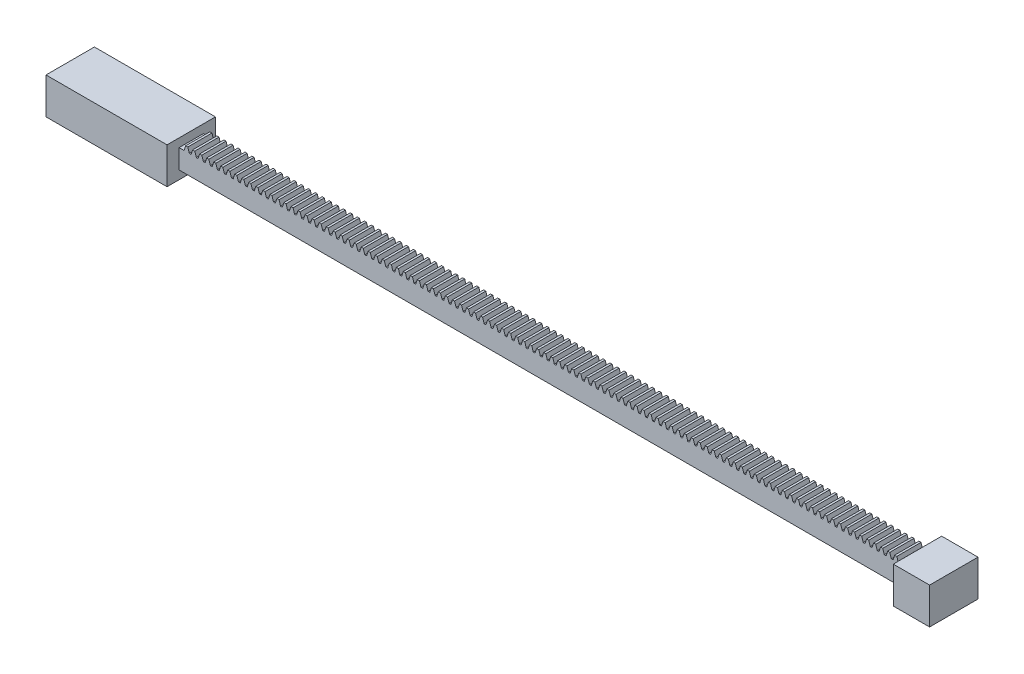
SolidWorks part; units mm, degrees
ref_plane "Front Plane" through (0, 0, 0) normal (0, 0, 1) x (1, 0, 0)
ref_plane "Top Plane" through (0, 0, 0) normal (0, 1, 0) x (1, 0, 0)
ref_plane "Right Plane" through (0, 0, 0) normal (1, 0, 0) x (0, 0, -1)
sketch "Sketch1" plane through (0, 0, 0) normal (0, 0, 1) x (1, 0, 0)
  line L0 (147.8394, 4) -> (148.4797, 6)
  line L1 (-150, 4) -> (150, 4)
  line L2 (-150, 4) -> (-150, -4)
  line L3 (-150, -4) -> (150, -4)
  line L4 (150, 4) -> (150, -4)
  line L5 (-150, 4) -> (150, -4) construction
  line L6 (-150, -4) -> (150, 4) construction
  line L7 (148.4797, 6) -> (149.3597, 6)
  line L8 (149.3597, 6) -> (150, 4)
  line L9 (144.9394, 4) -> (145.5797, 6)
  line L10 (145.5797, 6) -> (146.4597, 6)
  line L11 (146.4597, 6) -> (147.1, 4)
  line L12 (142.0394, 4) -> (142.6797, 6)
  line L13 (142.6797, 6) -> (143.5597, 6)
  line L14 (143.5597, 6) -> (144.2, 4)
  line L15 (139.1394, 4) -> (139.7797, 6)
  line L16 (139.7797, 6) -> (140.6597, 6)
  line L17 (140.6597, 6) -> (141.3, 4)
  line L18 (136.2394, 4) -> (136.8797, 6)
  line L19 (136.8797, 6) -> (137.7597, 6)
  line L20 (137.7597, 6) -> (138.4, 4)
  line L21 (133.3394, 4) -> (133.9797, 6)
  line L22 (133.9797, 6) -> (134.8597, 6)
  line L23 (134.8597, 6) -> (135.5, 4)
  line L24 (130.4394, 4) -> (131.0797, 6)
  line L25 (131.0797, 6) -> (131.9597, 6)
  line L26 (131.9597, 6) -> (132.6, 4)
  line L27 (127.5394, 4) -> (128.1797, 6)
  line L28 (128.1797, 6) -> (129.0597, 6)
  line L29 (129.0597, 6) -> (129.7, 4)
  line L30 (124.6394, 4) -> (125.2797, 6)
  line L31 (125.2797, 6) -> (126.1597, 6)
  line L32 (126.1597, 6) -> (126.8, 4)
  line L33 (121.7394, 4) -> (122.3797, 6)
  line L34 (122.3797, 6) -> (123.2597, 6)
  line L35 (123.2597, 6) -> (123.9, 4)
  line L36 (118.8394, 4) -> (119.4797, 6)
  line L37 (119.4797, 6) -> (120.3597, 6)
  line L38 (120.3597, 6) -> (121, 4)
  line L39 (115.9394, 4) -> (116.5797, 6)
  line L40 (116.5797, 6) -> (117.4597, 6)
  line L41 (117.4597, 6) -> (118.1, 4)
  line L42 (113.0394, 4) -> (113.6797, 6)
  line L43 (113.6797, 6) -> (114.5597, 6)
  line L44 (114.5597, 6) -> (115.2, 4)
  line L45 (110.1394, 4) -> (110.7797, 6)
  line L46 (110.7797, 6) -> (111.6597, 6)
  line L47 (111.6597, 6) -> (112.3, 4)
  line L48 (107.2394, 4) -> (107.8797, 6)
  line L49 (107.8797, 6) -> (108.7597, 6)
  line L50 (108.7597, 6) -> (109.4, 4)
  line L51 (104.3394, 4) -> (104.9797, 6)
  line L52 (104.9797, 6) -> (105.8597, 6)
  line L53 (105.8597, 6) -> (106.5, 4)
  line L54 (101.4394, 4) -> (102.0797, 6)
  line L55 (102.0797, 6) -> (102.9597, 6)
  line L56 (102.9597, 6) -> (103.6, 4)
  line L57 (98.5394, 4) -> (99.1797, 6)
  line L58 (99.1797, 6) -> (100.0597, 6)
  line L59 (100.0597, 6) -> (100.7, 4)
  line L60 (95.6394, 4) -> (96.2797, 6)
  line L61 (96.2797, 6) -> (97.1597, 6)
  line L62 (97.1597, 6) -> (97.8, 4)
  line L63 (92.7394, 4) -> (93.3797, 6)
  line L64 (93.3797, 6) -> (94.2597, 6)
  line L65 (94.2597, 6) -> (94.9, 4)
  line L66 (89.8394, 4) -> (90.4797, 6)
  line L67 (90.4797, 6) -> (91.3597, 6)
  line L68 (91.3597, 6) -> (92, 4)
  line L69 (86.9394, 4) -> (87.5797, 6)
  line L70 (87.5797, 6) -> (88.4597, 6)
  line L71 (88.4597, 6) -> (89.1, 4)
  line L72 (84.0394, 4) -> (84.6797, 6)
  line L73 (84.6797, 6) -> (85.5597, 6)
  line L74 (85.5597, 6) -> (86.2, 4)
  line L75 (81.1394, 4) -> (81.7797, 6)
  line L76 (81.7797, 6) -> (82.6597, 6)
  line L77 (82.6597, 6) -> (83.3, 4)
  line L78 (78.2394, 4) -> (78.8797, 6)
  line L79 (78.8797, 6) -> (79.7597, 6)
  line L80 (79.7597, 6) -> (80.4, 4)
  line L81 (75.3394, 4) -> (75.9797, 6)
  line L82 (75.9797, 6) -> (76.8597, 6)
  line L83 (76.8597, 6) -> (77.5, 4)
  line L84 (72.4394, 4) -> (73.0797, 6)
  line L85 (73.0797, 6) -> (73.9597, 6)
  line L86 (73.9597, 6) -> (74.6, 4)
  line L87 (69.5394, 4) -> (70.1797, 6)
  line L88 (70.1797, 6) -> (71.0597, 6)
  line L89 (71.0597, 6) -> (71.7, 4)
  line L90 (66.6394, 4) -> (67.2797, 6)
  line L91 (67.2797, 6) -> (68.1597, 6)
  line L92 (68.1597, 6) -> (68.8, 4)
  line L93 (63.7394, 4) -> (64.3797, 6)
  line L94 (64.3797, 6) -> (65.2597, 6)
  line L95 (65.2597, 6) -> (65.9, 4)
  line L96 (60.8394, 4) -> (61.4797, 6)
  line L97 (61.4797, 6) -> (62.3597, 6)
  line L98 (62.3597, 6) -> (63, 4)
  line L99 (57.9394, 4) -> (58.5797, 6)
  line L100 (58.5797, 6) -> (59.4597, 6)
  line L101 (59.4597, 6) -> (60.1, 4)
  line L102 (55.0394, 4) -> (55.6797, 6)
  line L103 (55.6797, 6) -> (56.5597, 6)
  line L104 (56.5597, 6) -> (57.2, 4)
  line L105 (52.1394, 4) -> (52.7797, 6)
  line L106 (52.7797, 6) -> (53.6597, 6)
  line L107 (53.6597, 6) -> (54.3, 4)
  line L108 (49.2394, 4) -> (49.8797, 6)
  line L109 (49.8797, 6) -> (50.7597, 6)
  line L110 (50.7597, 6) -> (51.4, 4)
  line L111 (46.3394, 4) -> (46.9797, 6)
  line L112 (46.9797, 6) -> (47.8597, 6)
  line L113 (47.8597, 6) -> (48.5, 4)
  line L114 (43.4394, 4) -> (44.0797, 6)
  line L115 (44.0797, 6) -> (44.9597, 6)
  line L116 (44.9597, 6) -> (45.6, 4)
  line L117 (40.5394, 4) -> (41.1797, 6)
  line L118 (41.1797, 6) -> (42.0597, 6)
  line L119 (42.0597, 6) -> (42.7, 4)
  line L120 (37.6394, 4) -> (38.2797, 6)
  line L121 (38.2797, 6) -> (39.1597, 6)
  line L122 (39.1597, 6) -> (39.8, 4)
  line L123 (34.7394, 4) -> (35.3797, 6)
  line L124 (35.3797, 6) -> (36.2597, 6)
  line L125 (36.2597, 6) -> (36.9, 4)
  line L126 (31.8394, 4) -> (32.4797, 6)
  line L127 (32.4797, 6) -> (33.3597, 6)
  line L128 (33.3597, 6) -> (34, 4)
  line L129 (28.9394, 4) -> (29.5797, 6)
  line L130 (29.5797, 6) -> (30.4597, 6)
  line L131 (30.4597, 6) -> (31.1, 4)
  line L132 (26.0394, 4) -> (26.6797, 6)
  line L133 (26.6797, 6) -> (27.5597, 6)
  line L134 (27.5597, 6) -> (28.2, 4)
  line L135 (23.1394, 4) -> (23.7797, 6)
  line L136 (23.7797, 6) -> (24.6597, 6)
  line L137 (24.6597, 6) -> (25.3, 4)
  line L138 (20.2394, 4) -> (20.8797, 6)
  line L139 (20.8797, 6) -> (21.7597, 6)
  line L140 (21.7597, 6) -> (22.4, 4)
  line L141 (17.3394, 4) -> (17.9797, 6)
  line L142 (17.9797, 6) -> (18.8597, 6)
  line L143 (18.8597, 6) -> (19.5, 4)
  line L144 (14.4394, 4) -> (15.0797, 6)
  line L145 (15.0797, 6) -> (15.9597, 6)
  line L146 (15.9597, 6) -> (16.6, 4)
  line L147 (11.5394, 4) -> (12.1797, 6)
  line L148 (12.1797, 6) -> (13.0597, 6)
  line L149 (13.0597, 6) -> (13.7, 4)
  line L150 (8.6394, 4) -> (9.2797, 6)
  line L151 (9.2797, 6) -> (10.1597, 6)
  line L152 (10.1597, 6) -> (10.8, 4)
  line L153 (5.7394, 4) -> (6.3797, 6)
  line L154 (6.3797, 6) -> (7.2597, 6)
  line L155 (7.2597, 6) -> (7.9, 4)
  line L156 (2.8394, 4) -> (3.4797, 6)
  line L157 (3.4797, 6) -> (4.3597, 6)
  line L158 (4.3597, 6) -> (5, 4)
  line L159 (-0.0606, 4) -> (0.5797, 6)
  line L160 (0.5797, 6) -> (1.4597, 6)
  line L161 (1.4597, 6) -> (2.1, 4)
  line L162 (-2.9606, 4) -> (-2.3203, 6)
  line L163 (-2.3203, 6) -> (-1.4403, 6)
  line L164 (-1.4403, 6) -> (-0.8, 4)
  line L165 (-5.8606, 4) -> (-5.2203, 6)
  line L166 (-5.2203, 6) -> (-4.3403, 6)
  line L167 (-4.3403, 6) -> (-3.7, 4)
  line L168 (-8.7606, 4) -> (-8.1203, 6)
  line L169 (-8.1203, 6) -> (-7.2403, 6)
  line L170 (-7.2403, 6) -> (-6.6, 4)
  line L171 (-11.6606, 4) -> (-11.0203, 6)
  line L172 (-11.0203, 6) -> (-10.1403, 6)
  line L173 (-10.1403, 6) -> (-9.5, 4)
  line L174 (-14.5606, 4) -> (-13.9203, 6)
  line L175 (-13.9203, 6) -> (-13.0403, 6)
  line L176 (-13.0403, 6) -> (-12.4, 4)
  line L177 (-17.4606, 4) -> (-16.8203, 6)
  line L178 (-16.8203, 6) -> (-15.9403, 6)
  line L179 (-15.9403, 6) -> (-15.3, 4)
  line L180 (-20.3606, 4) -> (-19.7203, 6)
  line L181 (-19.7203, 6) -> (-18.8403, 6)
  line L182 (-18.8403, 6) -> (-18.2, 4)
  line L183 (-23.2606, 4) -> (-22.6203, 6)
  line L184 (-22.6203, 6) -> (-21.7403, 6)
  line L185 (-21.7403, 6) -> (-21.1, 4)
  line L186 (-26.1606, 4) -> (-25.5203, 6)
  line L187 (-25.5203, 6) -> (-24.6403, 6)
  line L188 (-24.6403, 6) -> (-24, 4)
  line L189 (-29.0606, 4) -> (-28.4203, 6)
  line L190 (-28.4203, 6) -> (-27.5403, 6)
  line L191 (-27.5403, 6) -> (-26.9, 4)
  line L192 (-31.9606, 4) -> (-31.3203, 6)
  line L193 (-31.3203, 6) -> (-30.4403, 6)
  line L194 (-30.4403, 6) -> (-29.8, 4)
  line L195 (-34.8606, 4) -> (-34.2203, 6)
  line L196 (-34.2203, 6) -> (-33.3403, 6)
  line L197 (-33.3403, 6) -> (-32.7, 4)
  line L198 (-37.7606, 4) -> (-37.1203, 6)
  line L199 (-37.1203, 6) -> (-36.2403, 6)
  line L200 (-36.2403, 6) -> (-35.6, 4)
  line L201 (-40.6606, 4) -> (-40.0203, 6)
  line L202 (-40.0203, 6) -> (-39.1403, 6)
  line L203 (-39.1403, 6) -> (-38.5, 4)
  line L204 (-43.5606, 4) -> (-42.9203, 6)
  line L205 (-42.9203, 6) -> (-42.0403, 6)
  line L206 (-42.0403, 6) -> (-41.4, 4)
  line L207 (-46.4606, 4) -> (-45.8203, 6)
  line L208 (-45.8203, 6) -> (-44.9403, 6)
  line L209 (-44.9403, 6) -> (-44.3, 4)
  line L210 (-49.3606, 4) -> (-48.7203, 6)
  line L211 (-48.7203, 6) -> (-47.8403, 6)
  line L212 (-47.8403, 6) -> (-47.2, 4)
  line L213 (-52.2606, 4) -> (-51.6203, 6)
  line L214 (-51.6203, 6) -> (-50.7403, 6)
  line L215 (-50.7403, 6) -> (-50.1, 4)
  line L216 (-55.1606, 4) -> (-54.5203, 6)
  line L217 (-54.5203, 6) -> (-53.6403, 6)
  line L218 (-53.6403, 6) -> (-53, 4)
  line L219 (-58.0606, 4) -> (-57.4203, 6)
  line L220 (-57.4203, 6) -> (-56.5403, 6)
  line L221 (-56.5403, 6) -> (-55.9, 4)
  line L222 (-60.9606, 4) -> (-60.3203, 6)
  line L223 (-60.3203, 6) -> (-59.4403, 6)
  line L224 (-59.4403, 6) -> (-58.8, 4)
  line L225 (-63.8606, 4) -> (-63.2203, 6)
  line L226 (-63.2203, 6) -> (-62.3403, 6)
  line L227 (-62.3403, 6) -> (-61.7, 4)
  line L228 (-66.7606, 4) -> (-66.1203, 6)
  line L229 (-66.1203, 6) -> (-65.2403, 6)
  line L230 (-65.2403, 6) -> (-64.6, 4)
  line L231 (-69.6606, 4) -> (-69.0203, 6)
  line L232 (-69.0203, 6) -> (-68.1403, 6)
  line L233 (-68.1403, 6) -> (-67.5, 4)
  line L234 (-72.5606, 4) -> (-71.9203, 6)
  line L235 (-71.9203, 6) -> (-71.0403, 6)
  line L236 (-71.0403, 6) -> (-70.4, 4)
  line L237 (-75.4606, 4) -> (-74.8203, 6)
  line L238 (-74.8203, 6) -> (-73.9403, 6)
  line L239 (-73.9403, 6) -> (-73.3, 4)
  line L240 (-78.3606, 4) -> (-77.7203, 6)
  line L241 (-77.7203, 6) -> (-76.8403, 6)
  line L242 (-76.8403, 6) -> (-76.2, 4)
  line L243 (-81.2606, 4) -> (-80.6203, 6)
  line L244 (-80.6203, 6) -> (-79.7403, 6)
  line L245 (-79.7403, 6) -> (-79.1, 4)
  line L246 (-84.1606, 4) -> (-83.5203, 6)
  line L247 (-83.5203, 6) -> (-82.6403, 6)
  line L248 (-82.6403, 6) -> (-82, 4)
  line L249 (-87.0606, 4) -> (-86.4203, 6)
  line L250 (-86.4203, 6) -> (-85.5403, 6)
  line L251 (-85.5403, 6) -> (-84.9, 4)
  line L252 (-89.9606, 4) -> (-89.3203, 6)
  line L253 (-89.3203, 6) -> (-88.4403, 6)
  line L254 (-88.4403, 6) -> (-87.8, 4)
  line L255 (-92.8606, 4) -> (-92.2203, 6)
  line L256 (-92.2203, 6) -> (-91.3403, 6)
  line L257 (-91.3403, 6) -> (-90.7, 4)
  line L258 (-95.7606, 4) -> (-95.1203, 6)
  line L259 (-95.1203, 6) -> (-94.2403, 6)
  line L260 (-94.2403, 6) -> (-93.6, 4)
  line L261 (-98.6606, 4) -> (-98.0203, 6)
  line L262 (-98.0203, 6) -> (-97.1403, 6)
  line L263 (-97.1403, 6) -> (-96.5, 4)
  line L264 (-101.5606, 4) -> (-100.9203, 6)
  line L265 (-100.9203, 6) -> (-100.0403, 6)
  line L266 (-100.0403, 6) -> (-99.4, 4)
  line L267 (-104.4606, 4) -> (-103.8203, 6)
  line L268 (-103.8203, 6) -> (-102.9403, 6)
  line L269 (-102.9403, 6) -> (-102.3, 4)
  line L270 (-107.3606, 4) -> (-106.7203, 6)
  line L271 (-106.7203, 6) -> (-105.8403, 6)
  line L272 (-105.8403, 6) -> (-105.2, 4)
  line L273 (-110.2606, 4) -> (-109.6203, 6)
  line L274 (-109.6203, 6) -> (-108.7403, 6)
  line L275 (-108.7403, 6) -> (-108.1, 4)
  line L276 (-113.1606, 4) -> (-112.5203, 6)
  line L277 (-112.5203, 6) -> (-111.6403, 6)
  line L278 (-111.6403, 6) -> (-111, 4)
  line L279 (-116.0606, 4) -> (-115.4203, 6)
  line L280 (-115.4203, 6) -> (-114.5403, 6)
  line L281 (-114.5403, 6) -> (-113.9, 4)
  line L282 (-118.9606, 4) -> (-118.3203, 6)
  line L283 (-118.3203, 6) -> (-117.4403, 6)
  line L284 (-117.4403, 6) -> (-116.8, 4)
  line L285 (-121.8606, 4) -> (-121.2203, 6)
  line L286 (-121.2203, 6) -> (-120.3403, 6)
  line L287 (-120.3403, 6) -> (-119.7, 4)
  line L288 (-124.7606, 4) -> (-124.1203, 6)
  line L289 (-124.1203, 6) -> (-123.2403, 6)
  line L290 (-123.2403, 6) -> (-122.6, 4)
  line L291 (-127.6606, 4) -> (-127.0203, 6)
  line L292 (-127.0203, 6) -> (-126.1403, 6)
  line L293 (-126.1403, 6) -> (-125.5, 4)
  line L294 (-130.5606, 4) -> (-129.9203, 6)
  line L295 (-129.9203, 6) -> (-129.0403, 6)
  line L296 (-129.0403, 6) -> (-128.4, 4)
  line L297 (-133.4606, 4) -> (-132.8203, 6)
  line L298 (-132.8203, 6) -> (-131.9403, 6)
  line L299 (-131.9403, 6) -> (-131.3, 4)
  line L300 (-136.3606, 4) -> (-135.7203, 6)
  line L301 (-135.7203, 6) -> (-134.8403, 6)
  line L302 (-134.8403, 6) -> (-134.2, 4)
  line L303 (-139.2606, 4) -> (-138.6203, 6)
  line L304 (-138.6203, 6) -> (-137.7403, 6)
  line L305 (-137.7403, 6) -> (-137.1, 4)
  line L306 (-142.1606, 4) -> (-141.5203, 6)
  line L307 (-141.5203, 6) -> (-140.6403, 6)
  line L308 (-140.6403, 6) -> (-140, 4)
  line L309 (-145.0606, 4) -> (-144.4203, 6)
  line L310 (-144.4203, 6) -> (-143.5403, 6)
  line L311 (-143.5403, 6) -> (-142.9, 4)
  line L312 (-147.9606, 4) -> (-147.3203, 6)
  line L313 (-147.3203, 6) -> (-146.4403, 6)
  line L314 (-146.4403, 6) -> (-145.8, 4)
  point P0 (0, 0)
  dimension "D1" = 8
  dimension "D2" = 300
  dimension "D3" = 0.88
  dimension "D4" = 2
  dimension "D5" = 2.1
  dimension "D6" = 2.1606
  dimension "D7" = 103
extrude "Boss-Extrude1" add sketch "Sketch1" along normal blind 10 contours L4 L1
sketch "Sketch2" plane through (0, 0, 10) normal (0, 0, 1) x (1, 0, 0)
  line L3 (147.8394, 4) -> (148.4797, 6)
  line L4 (150, -4) -> (150, 4)
  line L5 (150, 4) -> (-150, 4)
  line L6 (-150, 4) -> (-150, -4)
  line L7 (-150, -4) -> (150, -4)
  line L9 (150, 4) -> (147.8394, 4)
  line L12 (148.4797, 6) -> (149.3597, 6)
  line L13 (149.3597, 6) -> (150, 4)
  dimension "D1" = 0
extrude "Boss-Extrude2" add sketch "Sketch2" against normal blind 10
pattern_linear "LPattern1" count 103 spacing 2.9 along (-1, 0, 0) of "Boss-Extrude2"
sketch "Sketch3" plane through (150, 0, 0) normal (1, 0, 0) x (0, 0, -1)
  line L0 (-10, -4) -> (0, -4) construction
  line L1 (-15, 7.5) -> (5, 7.5)
  line L2 (-15, 7.5) -> (-15, -7.5)
  line L3 (-15, -7.5) -> (5, -7.5)
  line L4 (5, 7.5) -> (5, -7.5)
  line L5 (-15, 7.5) -> (5, -7.5) construction
  line L6 (-15, -7.5) -> (5, 7.5) construction
  point P0 (-5, 0)
  point P8 (-5, -4)
  dimension "D1" = 20
  dimension "D2" = 15
extrude "Boss-Extrude3" add sketch "Sketch3" along normal blind 15
sketch "Sketch4" plane through (-150, 0, 0) normal (-1, 0, 0) x (0, 0, 1)
  line L0 (-5, -7.5) -> (-5, 7.5) construction
  line L1 (-5, -7.5) -> (-5, 7.5)
  line L2 (15, -7.5) -> (-5, -7.5) construction
  line L3 (15, 7.5) -> (15, -7.5) construction
  line L4 (-5, 7.5) -> (15, 7.5) construction
  line L5 (15, -7.5) -> (-5, -7.5)
  line L6 (15, 7.5) -> (15, -7.5)
  line L7 (-5, 7.5) -> (15, 7.5)
extrude "Boss-Extrude4" add sketch "Sketch4" along normal blind 50
sketch "Sketch5" plane through (-200, 0, 0) normal (-1, 0, 0) x (0, 0, 1)
  line L0 (-7, -16.5) -> (17, -16.5) construction
  line L2 (-5, -7.5) -> (15, -7.5) construction
  circle A0 centre (5, -16.5) radius 9
  circle A1 centre (5, -16.5) radius 12
  dimension "D1" = 3
extrude "Boss-Extrude6" [suppressed] add sketch "Sketch5" against normal blind 30
